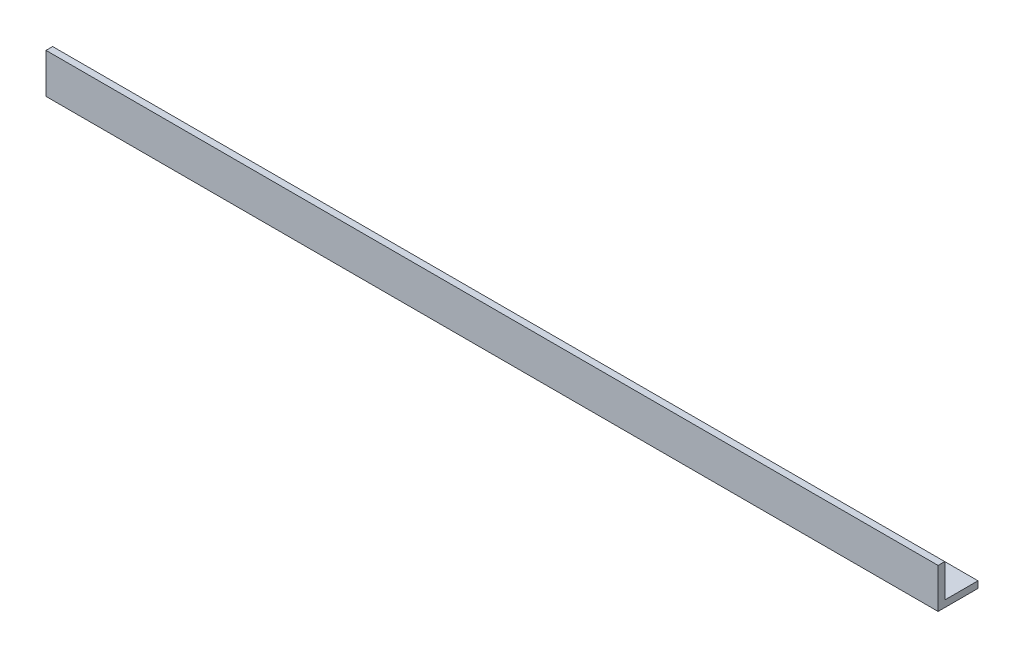
SolidWorks part; units mm, degrees
ref_plane "Front Plane" through (0, 0, 0) normal (0, 0, 1) x (1, 0, 0)
ref_plane "Top Plane" through (0, 0, 0) normal (0, 1, 0) x (1, 0, 0)
ref_plane "Right Plane" through (0, 0, 0) normal (1, 0, 0) x (0, 0, -1)
sketch "Sketch1" plane through (0, 0, 0) normal (1, 0, 0) x (0, 0, -1)
  line L0 (0, 0) -> (0, 19.05)
  line L1 (0, 19.05) -> (3.175, 19.05)
  line L2 (3.175, 19.05) -> (3.175, 3.175)
  line L3 (3.175, 3.175) -> (19.05, 3.175)
  line L4 (19.05, 3.175) -> (19.05, 0)
  line L5 (19.05, 0) -> (0, 0)
extrude "Boss-Extrude1" add sketch "Sketch1" along normal blind 426
